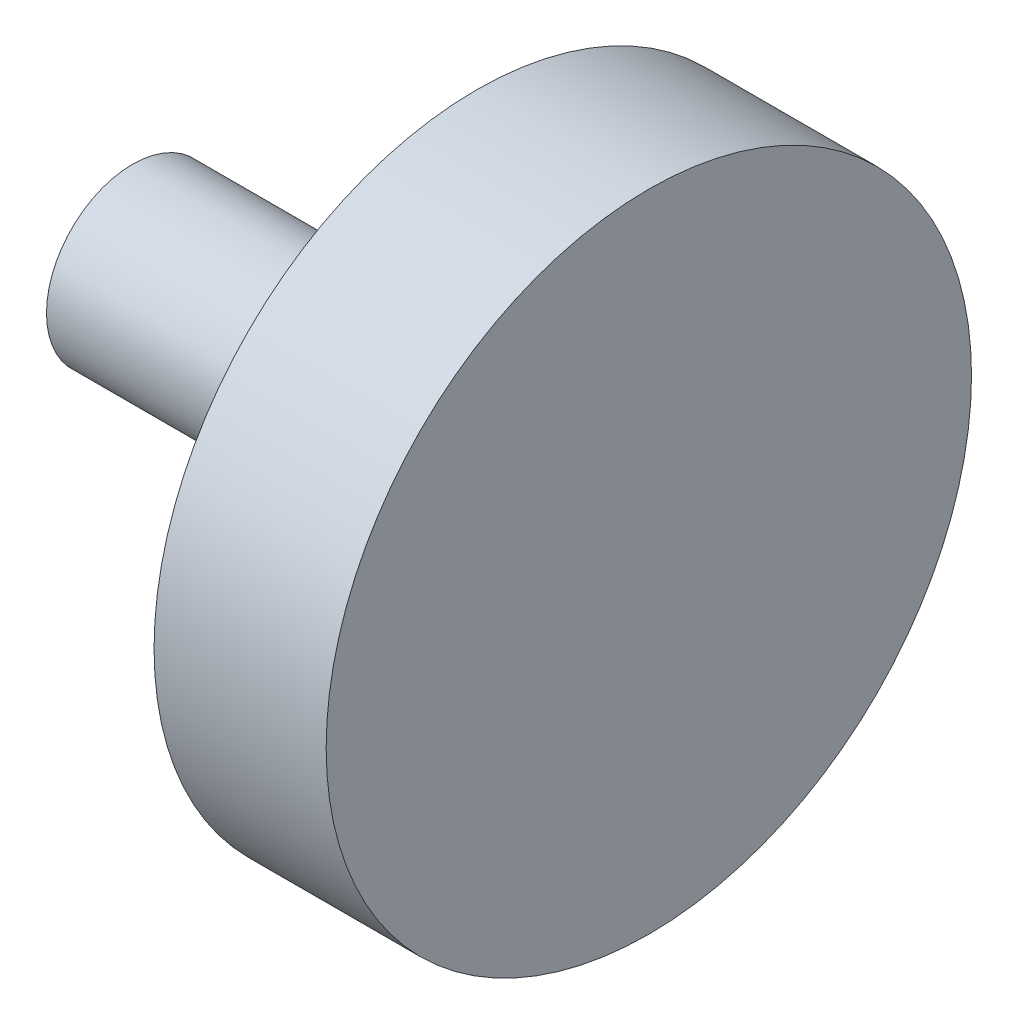
SolidWorks part; units mm, degrees
ref_plane "Front Plane" through (0, 0, 0) normal (0, 0, 1) x (1, 0, 0)
ref_plane "Top Plane" through (0, 0, 0) normal (0, 1, 0) x (1, 0, 0)
ref_plane "Right Plane" through (0, 0, 0) normal (1, 0, 0) x (0, 0, -1)
sketch "Sketch1" plane through (0, 0, 0) normal (1, 0, 0) x (0, 0, -1)
  circle A0 centre (0, 0) radius 7.5
  dimension "D1" = 15
extrude "Boss-Extrude1" add sketch "Sketch1" along normal blind 4
sketch "Sketch2" plane through (0, 0, 0) normal (-1, 0, 0) x (0, 0, 1)
  circle A0 centre (0, 0) radius 2
  dimension "D1" = 4
extrude "Boss-Extrude3" add sketch "Sketch2" along normal blind 8
